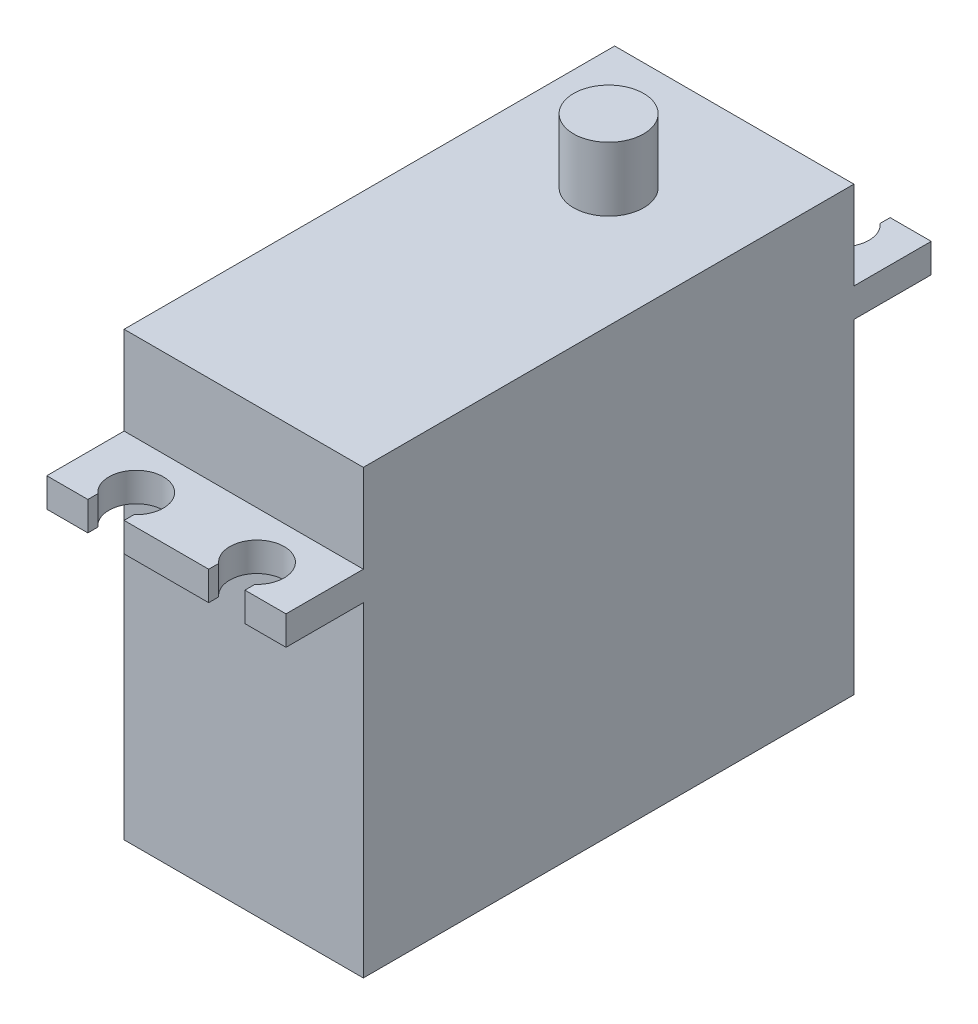
SolidWorks part; units mm, degrees
ref_plane "Front Plane" through (0, 0, 0) normal (0, 0, 1) x (1, 0, 0)
ref_plane "Top Plane" through (0, 0, 0) normal (0, 1, 0) x (1, 0, 0)
ref_plane "Right Plane" through (0, 0, 0) normal (1, 0, 0) x (0, 0, -1)
sketch "Sketch2" plane through (0, 0, 0) normal (1, 0, 0) x (0, 0, -1)
  line L1 (-20.3, 18.3) -> (20.3, 18.3)
  line L2 (-20.3, 18.3) -> (-20.3, -18.3)
  line L3 (-20.3, -18.3) -> (20.3, -18.3)
  line L4 (20.3, 18.3) -> (20.3, -18.3)
  line L5 (-20.3, 18.3) -> (20.3, -18.3) construction
  line L6 (-20.3, -18.3) -> (20.3, 18.3) construction
  line L7 (20.3, 11) -> (26.7, 11)
  line L8 (20.3, 11) -> (20.3, 8.6)
  line L9 (20.3, 8.6) -> (26.7, 8.6)
  line L10 (26.7, 11) -> (26.7, 8.6)
  line L11 (-20.3, 11) -> (-26.7, 11)
  line L12 (-20.3, 11) -> (-20.3, 8.6)
  line L13 (-20.3, 8.6) -> (-26.7, 8.6)
  line L14 (-26.7, 11) -> (-26.7, 8.6)
  line L16 (-26.7, 9.8) -> (26.7, 9.8) construction
  line L17 (7, 18.3) -> (12.8, 18.3)
  line L18 (7, 18.3) -> (7, 23.6)
  line L19 (7, 23.6) -> (12.8, 23.6)
  line L20 (12.8, 18.3) -> (12.8, 23.6)
  point P0 (0, 0)
  point P15 (9.9, 23.6)
  point P22 (0, 9.8)
  dimension "D1" = 26.9
  dimension "D2" = 40.6
  dimension "D3" = 5.3
  dimension "D4" = 53.4
  dimension "D5" = 36.6
  dimension "D6" = 2.4
  dimension "D7" = 5.8
  dimension "D8" = 10.4
extrude "Boss-Extrude1" add sketch "Sketch2" along normal blind 19.8 contours L4 L1 L2 L3 | L11 L14 L13 L2 | L1 L20 L19 L18 | L10 L7 L4 L9
sketch "Sketch3" plane through (0, 18.3, 0) normal (0, 1, 0) x (1, 0, 0)
  line L0 (19.8, 12.8) -> (0, 12.8) construction
  line L1 (19.8, 7) -> (12.8, 7)
  line L2 (19.8, 7) -> (19.8, 12.8)
  line L3 (19.8, 12.8) -> (12.8, 12.8)
  line L4 (12.8, 7) -> (12.8, 12.8)
  line L5 (19.8, 12.8) -> (0, 12.8) construction
  line L6 (0, 7) -> (7, 7)
  line L7 (0, 7) -> (0, 12.8)
  line L8 (0, 12.8) -> (7, 12.8)
  line L9 (7, 7) -> (7, 12.8)
  line L10 (19.8, 26.7) -> (0, 26.7) construction
  line L11 (12.8, 12.8) -> (7, 12.8)
  line L12 (12.8, 7) -> (7, 7)
  circle A0 centre (9.9, 9.9) radius 2.9
  point P15 (7, 9.9)
  point P21 (9.9, 26.7)
  line M7 (19.8, 7) -> (0, 7)
extrude "Cut-Extrude1" cut sketch "Sketch3" along normal up to surface (5.3 mm away) contours A0 L4 M7 | A0 L4 L11 | A0 L11 L9 | A0 L9 L12 | L9 L8 L7 M7 | L4 L2 L3 M7 up to face at (9.9, 23.6, -9.9)
sketch "Sketch4" plane through (0, 11, 0) normal (0, 1, 0) x (1, 0, 0)
  line L0 (14.9, 24.2) -> (14.9, -24.2) construction
  line L1 (14.9, -24.2) -> (4.9, -24.2) construction
  line L2 (4.9, -24.2) -> (4.9, 24.2) construction
  line L3 (4.9, 24.2) -> (14.9, 24.2) construction
  line L4 (19.8, 26.7) -> (0, 26.7) construction
  line L5 (19.8, -20.3) -> (19.8, 20.3) construction
  line L6 (19.8, -26.7) -> (0, -26.7) construction
  line L7 (6.4, 26.7) -> (3.4, 26.7)
  line L8 (6.4, 26.7) -> (6.4, 25.8771)
  line L9 (6.4, 25.8771) -> (3.4, 25.8771)
  line L10 (3.4, 26.7) -> (3.4, 25.8771)
  line L11 (16.4, 26.7) -> (13.4, 26.7)
  line L12 (16.4, 26.7) -> (16.4, 25.8771)
  line L13 (16.4, 25.8771) -> (13.4, 25.8771)
  line L14 (13.4, 26.7) -> (13.4, 25.8771)
  line L15 (16.4, -26.7) -> (13.4, -26.7)
  line L16 (16.4, -26.7) -> (16.4, -25.8771)
  line L17 (16.4, -25.8771) -> (13.4, -25.8771)
  line L18 (13.4, -26.7) -> (13.4, -25.8771)
  line L20 (6.4, -26.7) -> (3.4, -26.7)
  line L21 (6.4, -26.7) -> (6.4, -25.8771)
  line L22 (6.4, -25.8771) -> (3.4, -25.8771)
  line L23 (3.4, -26.7) -> (3.4, -25.8771)
  circle A0 centre (14.9, 24.2) radius 2.25
  circle A1 centre (4.9, 24.2) radius 2.25
  circle A2 centre (14.9, -24.2) radius 2.25
  circle A3 centre (4.9, -24.2) radius 2.25
  point P8 (9.9, 24.2)
  point P11 (9.9, 26.7)
  point P13 (14.9, 0)
  point P16 (19.8, 0)
  line M8 (19.8, 26.7) -> (0, 26.7)
  dimension "D3" = 4.5
  dimension "D1" = 10
  dimension "D2" = 48.4
  dimension "D4" = 3
extrude "Cut-Extrude2" cut sketch "Sketch4" against normal through all contours L13 A0 | L13 A0 | A0 L12 L14 M8 | L9 A1 | L9 A1 | A1 L8 L10 M8 | L17 A2 | A2 L18 L15 L16 | L17 A2 | L22 A3 | A3 L23 L20 L21 | L22 A3
